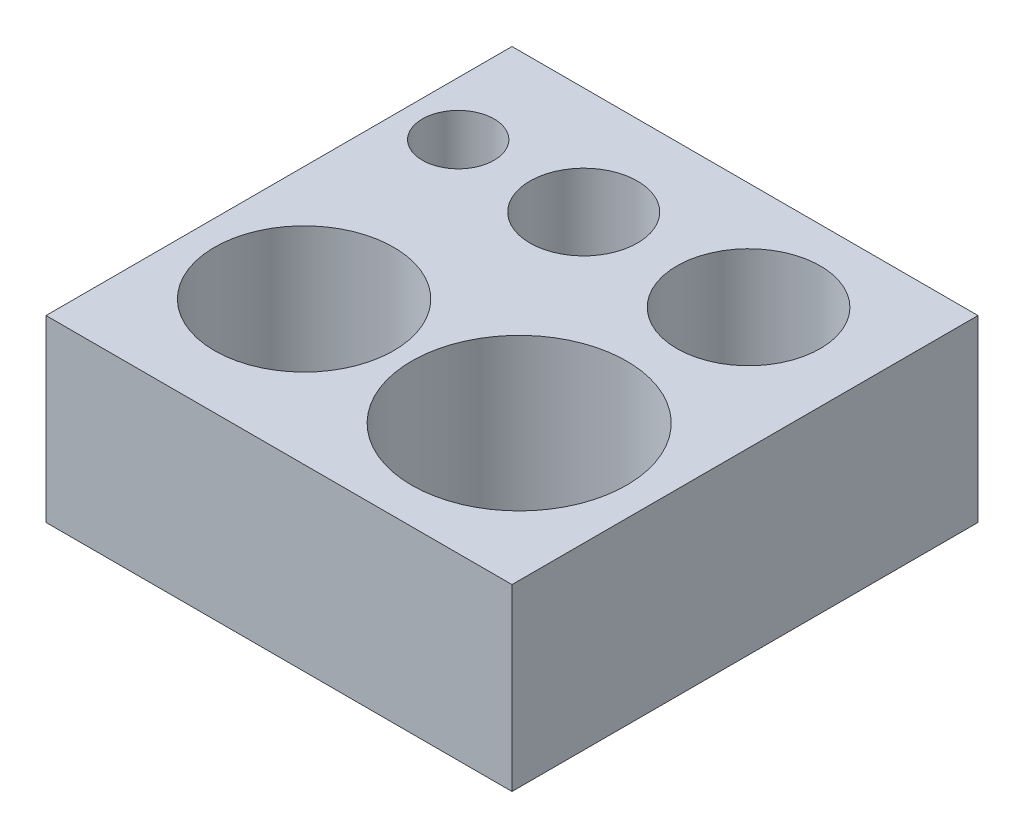
SolidWorks part; units mm, degrees
ref_plane "Front Plane" through (0, 0, 0) normal (0, 0, 1) x (1, 0, 0)
ref_plane "Top Plane" through (0, 0, 0) normal (0, 1, 0) x (1, 0, 0)
ref_plane "Right Plane" through (0, 0, 0) normal (1, 0, 0) x (0, 0, -1)
sketch "Sketch1" plane through (0, 0, 0) normal (0, 1, 0) x (1, 0, 0)
  line L0 (0, 10) -> (13, 10) construction
  line L1 (0, 0) -> (13, 0)
  line L2 (0, 0) -> (0, 13)
  line L3 (0, 13) -> (13, 13)
  line L4 (13, 0) -> (13, 13)
  line L5 (0, 4) -> (13, 4) construction
  circle A0 centre (1.5, 10) radius 1
  circle A1 centre (5, 10) radius 1.5
  circle A2 centre (9.6, 10) radius 2
  circle A4 centre (3.2, 4) radius 2.5
  circle A5 centre (9.2, 4) radius 3
  point P11 (9.4745, 10)
  point P12 (8.8678, 4)
  point P17 (2.9857, 4)
  point P23 (0, 0)
  point P24 (0, 0)
  point P25 (0, 0)
  point P26 (0, 0)
  dimension "D1" = 2
  dimension "D2" = 3
  dimension "D4" = 4
  dimension "D5" = 5
  dimension "D6" = 6
  dimension "D3" = 13
  dimension "D7" = 3
  dimension "D8" = 4
  dimension "D9" = 13
  dimension "D10" = 3.8
  dimension "D11" = 3.2
  dimension "D12" = 1.5
  dimension "D13" = 5
  dimension "D14" = 3.4
extrude "Boss-Extrude1" add sketch "Sketch1" along normal blind 5
